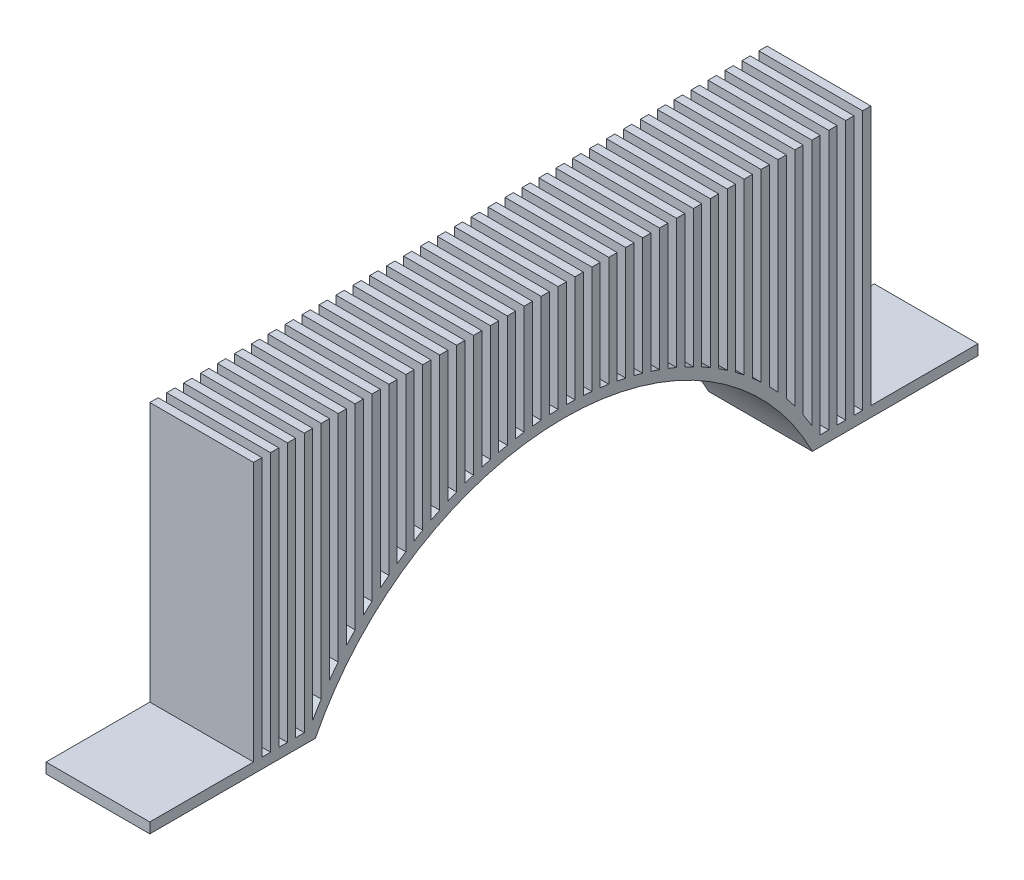
SolidWorks part; units mm, degrees
material "6061 Alloy"
ref_plane "Front Plane" through (0, 0, 0) normal (0, 0, 1) x (1, 0, 0)
ref_plane "Top Plane" through (0, 0, 0) normal (0, 1, 0) x (1, 0, 0)
ref_plane "Right Plane" through (0, 0, 0) normal (1, 0, 0) x (0, 0, -1)
sketch "Sketch1" plane through (0, 0, 0) normal (1, 0, 0) x (0, 0, -1)
  line L0 (18.792, 0) -> (29.9, 0)
  line L1 (-18.792, 0) -> (-29.9, 0)
  line L2 (-21.8, -11.05) -> (21.8, -11.05)
  line L3 (-29.9, 0) -> (-29.9, -11.05)
  line L4 (-29.9, -11.05) -> (-21.8, -11.05)
  line L5 (21.8, -11.05) -> (29.9, -11.05)
  line L6 (29.9, -11.05) -> (29.9, 0)
  line L7 (-29.9, 0) -> (-29.9, 1)
  line L8 (-29.9, 1) -> (-23.9382, 1)
  line L9 (23.9382, 1) -> (29.9, 1)
  line L10 (-24.5466, 2) -> (-39.9, 2)
  line L163 (-39.9, 2) -> (-39.9, 1)
  line L164 (-39.9, 1) -> (-23.9382, 1)
  line L165 (24.5466, 2) -> (39.9, 2)
  line L166 (29.9, 1) -> (29.9, 0)
  line L167 (39.9, 2) -> (39.9, 1)
  line L168 (39.9, 1) -> (23.9382, 1)
  line L169 (-28.27, 2) -> (-28.27, 27)
  line L174 (-29.9, 2) -> (-29.1, 2)
  line L175 (-29.9, 2) -> (-29.9, 27)
  line L176 (-29.9, 27) -> (-29.1, 27)
  line L177 (-29.1, 2) -> (-29.1, 27)
  line L178 (-28.27, 2) -> (-27.47, 2)
  line L179 (-27.47, 2) -> (-27.47, 27)
  line L180 (-28.27, 27) -> (-27.47, 27)
  line L181 (-26.64, 2) -> (-26.64, 27)
  line L182 (-26.64, 2) -> (-25.84, 2)
  line L183 (-25.84, 2) -> (-25.84, 27)
  line L184 (-26.64, 27) -> (-25.84, 27)
  line L185 (-25.01, 2) -> (-25.01, 27)
  line L186 (-25.01, 2) -> (-24.21, 2)
  line L187 (-24.21, 2) -> (-24.21, 27)
  line L188 (-25.01, 27) -> (-24.21, 27)
  line L189 (-23.38, 2) -> (-23.38, 27)
  line L190 (-23.38, 2) -> (-22.58, 2)
  line L191 (-22.58, 2) -> (-22.58, 27)
  line L192 (-23.38, 27) -> (-22.58, 27)
  line L193 (-21.75, 2) -> (-21.75, 27)
  line L194 (-21.75, 2) -> (-20.95, 2)
  line L195 (-20.95, 2) -> (-20.95, 27)
  line L196 (-21.75, 27) -> (-20.95, 27)
  line L197 (-20.12, 2) -> (-20.12, 27)
  line L198 (-20.12, 2) -> (-19.32, 2)
  line L199 (-19.32, 2) -> (-19.32, 27)
  line L200 (-20.12, 27) -> (-19.32, 27)
  line L201 (-18.49, 2) -> (-18.49, 27)
  line L202 (-18.49, 2) -> (-17.69, 2)
  line L203 (-17.69, 2) -> (-17.69, 27)
  line L204 (-18.49, 27) -> (-17.69, 27)
  line L205 (-16.86, 2) -> (-16.86, 27)
  line L206 (-16.86, 2) -> (-16.06, 2)
  line L207 (-16.06, 2) -> (-16.06, 27)
  line L208 (-16.86, 27) -> (-16.06, 27)
  line L209 (-15.23, 2) -> (-15.23, 27)
  line L210 (-15.23, 2) -> (-14.43, 2)
  line L211 (-14.43, 2) -> (-14.43, 27)
  line L212 (-15.23, 27) -> (-14.43, 27)
  line L213 (-13.6, 2) -> (-13.6, 27)
  line L214 (-13.6, 2) -> (-12.8, 2)
  line L215 (-12.8, 2) -> (-12.8, 27)
  line L216 (-13.6, 27) -> (-12.8, 27)
  line L217 (-11.97, 2) -> (-11.97, 27)
  line L218 (-11.97, 2) -> (-11.17, 2)
  line L219 (-11.17, 2) -> (-11.17, 27)
  line L220 (-11.97, 27) -> (-11.17, 27)
  line L221 (-10.34, 2) -> (-10.34, 27)
  line L222 (-10.34, 2) -> (-9.54, 2)
  line L223 (-9.54, 2) -> (-9.54, 27)
  line L224 (-10.34, 27) -> (-9.54, 27)
  line L225 (-8.71, 2) -> (-8.71, 27)
  line L226 (-8.71, 2) -> (-7.91, 2)
  line L227 (-7.91, 2) -> (-7.91, 27)
  line L228 (-8.71, 27) -> (-7.91, 27)
  line L229 (-7.08, 2) -> (-7.08, 27)
  line L230 (-7.08, 2) -> (-6.28, 2)
  line L231 (-6.28, 2) -> (-6.28, 27)
  line L232 (-7.08, 27) -> (-6.28, 27)
  line L233 (-5.45, 2) -> (-5.45, 27)
  line L234 (-5.45, 2) -> (-4.65, 2)
  line L235 (-4.65, 2) -> (-4.65, 27)
  line L236 (-5.45, 27) -> (-4.65, 27)
  line L237 (-3.82, 2) -> (-3.82, 27)
  line L238 (-3.82, 2) -> (-3.02, 2)
  line L239 (-3.02, 2) -> (-3.02, 27)
  line L240 (-3.82, 27) -> (-3.02, 27)
  line L241 (-2.19, 2) -> (-2.19, 27)
  line L242 (-2.19, 2) -> (-1.39, 2)
  line L243 (-1.39, 2) -> (-1.39, 27)
  line L244 (-2.19, 27) -> (-1.39, 27)
  line L245 (-0.56, 2) -> (-0.56, 27)
  line L246 (-0.56, 2) -> (0.24, 2)
  line L247 (0.24, 2) -> (0.24, 27)
  line L248 (-0.56, 27) -> (0.24, 27)
  line L249 (1.07, 2) -> (1.07, 27)
  line L250 (1.07, 2) -> (1.87, 2)
  line L251 (1.87, 2) -> (1.87, 27)
  line L252 (1.07, 27) -> (1.87, 27)
  line L253 (2.7, 2) -> (2.7, 27)
  line L254 (2.7, 2) -> (3.5, 2)
  line L255 (3.5, 2) -> (3.5, 27)
  line L256 (2.7, 27) -> (3.5, 27)
  line L257 (4.33, 2) -> (4.33, 27)
  line L258 (4.33, 2) -> (5.13, 2)
  line L259 (5.13, 2) -> (5.13, 27)
  line L260 (4.33, 27) -> (5.13, 27)
  line L261 (5.96, 2) -> (5.96, 27)
  line L262 (5.96, 2) -> (6.76, 2)
  line L263 (6.76, 2) -> (6.76, 27)
  line L264 (5.96, 27) -> (6.76, 27)
  line L265 (7.59, 2) -> (7.59, 27)
  line L266 (7.59, 2) -> (8.39, 2)
  line L267 (8.39, 2) -> (8.39, 27)
  line L268 (7.59, 27) -> (8.39, 27)
  line L269 (9.22, 2) -> (9.22, 27)
  line L270 (9.22, 2) -> (10.02, 2)
  line L271 (10.02, 2) -> (10.02, 27)
  line L272 (9.22, 27) -> (10.02, 27)
  line L273 (10.85, 2) -> (10.85, 27)
  line L274 (10.85, 2) -> (11.65, 2)
  line L275 (11.65, 2) -> (11.65, 27)
  line L276 (10.85, 27) -> (11.65, 27)
  line L277 (12.48, 2) -> (12.48, 27)
  line L278 (12.48, 2) -> (13.28, 2)
  line L279 (13.28, 2) -> (13.28, 27)
  line L280 (12.48, 27) -> (13.28, 27)
  line L281 (14.11, 2) -> (14.11, 27)
  line L282 (14.11, 2) -> (14.91, 2)
  line L283 (14.91, 2) -> (14.91, 27)
  line L284 (14.11, 27) -> (14.91, 27)
  line L285 (15.74, 2) -> (15.74, 27)
  line L286 (15.74, 2) -> (16.54, 2)
  line L287 (16.54, 2) -> (16.54, 27)
  line L288 (15.74, 27) -> (16.54, 27)
  line L289 (17.37, 2) -> (17.37, 27)
  line L290 (17.37, 2) -> (18.17, 2)
  line L291 (18.17, 2) -> (18.17, 27)
  line L292 (17.37, 27) -> (18.17, 27)
  line L293 (19, 2) -> (19, 27)
  line L294 (19, 2) -> (19.8, 2)
  line L295 (19.8, 2) -> (19.8, 27)
  line L296 (19, 27) -> (19.8, 27)
  line L297 (20.63, 2) -> (20.63, 27)
  line L298 (20.63, 2) -> (21.43, 2)
  line L299 (21.43, 2) -> (21.43, 27)
  line L300 (20.63, 27) -> (21.43, 27)
  line L301 (22.26, 2) -> (22.26, 27)
  line L302 (22.26, 2) -> (23.06, 2)
  line L303 (23.06, 2) -> (23.06, 27)
  line L304 (22.26, 27) -> (23.06, 27)
  line L305 (23.89, 2) -> (23.89, 27)
  line L306 (23.89, 2) -> (24.69, 2)
  line L307 (24.69, 2) -> (24.69, 27)
  line L308 (23.89, 27) -> (24.69, 27)
  line L309 (25.52, 2) -> (25.52, 27)
  line L310 (25.52, 2) -> (26.32, 2)
  line L311 (26.32, 2) -> (26.32, 27)
  line L312 (25.52, 27) -> (26.32, 27)
  line L313 (27.15, 2) -> (27.15, 27)
  line L314 (27.15, 2) -> (27.95, 2)
  line L315 (27.95, 2) -> (27.95, 27)
  line L316 (27.15, 27) -> (27.95, 27)
  line L317 (28.78, 2) -> (28.78, 27)
  line L318 (28.78, 2) -> (29.58, 2)
  line L319 (29.58, 2) -> (29.58, 27)
  line L320 (28.78, 27) -> (29.58, 27)
  arc A0 (21.8, -11.05) -> (-21.8, -11.05) centre (0, -11.05) ccw
  arc A3 (23.9382, 1) -> (-23.9382, 1) centre (0, -11.05) ccw
  arc A4 (23.3139, 0) -> (-23.3139, 0) centre (0, -11.05) ccw
  arc A5 (24.5466, 2) -> (-24.5466, 2) centre (0, -11.05) ccw
  point P47 (34.4187, -11.05)
  dimension "D1" = 21.8
  dimension "D5" = 25
  dimension "D10" = 1
  dimension "D7" = 0.8
  dimension "D11" = 1
  dimension "D2" = 11.05
  dimension "D3" = 8.1
  dimension "D4" = 8.1
  dimension "D6" = 1
  dimension "D8" = 1
  dimension "D12" = 10
  dimension "D9" = 1
  dimension "D13" = 10
  dimension "D14" = 37
extrude "Boss-Extrude1" add sketch "Sketch1" along normal blind 10 contours L184 L181 L10 L183 | A5 L195 L196 L193 | A5 L199 L200 L197 | A5 L203 L204 L201 | A5 L207 L208 L205 | A5 L211 L212 L209 | L10 L177 L176 L175 | A5 L187 L188 L185 L10 | A5 L191 L192 L189 | A5 L215 L216 L213 | A5 L219 L220 L217 | A5 L223 L224 L221 | A5 L227 L228 L225 | A5 L231 L232 L229 | A5 L235 L236 L233 | A5 L239 L240 L237 | A5 L243 L244 L241 | A5 L247 L248 L245 | A5 L251 L252 L249 | A5 L255 L256 L253 | A5 L259 L260 L257 | A5 L263 L264 L261 | A5 L267 L268 L265 | A5 L271 L272 L269 | A5 L275 L276 L273 | A5 L279 L280 L277 | A5 L283 L284 L281 | A5 L287 L288 L285 | A5 L291 L292 L289 | A5 L295 L296 L293 | A5 L299 L300 L297 | A5 L303 L304 L301 | A5 L165 L307 L308 L305 | L312 L309 L165 L311 | L316 L313 L165 L315 | L305 A5 L303 A3 L9 L168 L167 L165 L306 | L306 A5 L305 | L303 A5 L301 A3 | L301 A5 L299 A3 | L299 A5 L297 A3 | L297 A5 L295 A3 | L295 A5 L293 A3 | L293 A5 L291 A3 | L291 A5 L289 A3 | L289 A5 L287 A3 | L189 A5 L187 L186 L10 L163 L164 L8 A3 | L191 A5 L189 A3 | L187 A5 L186 | L193 A5 L191 A3 | L195 A5 L193 A3 | L197 A5 L195 A3 | L199 A5 L197 A3 | L201 A5 L199 A3 | L203 A5 L201 A3 | L205 A5 L203 A3 | L207 A5 L205 A3 | L209 A5 L207 A3 | L211 A5 L209 A3 | L213 A5 L211 A3 | L215 A5 L213 A3 | L217 A5 L215 A3 | L221 A5 L219 A3 | L223 A5 L221 A3 | L225 A5 L223 A3 | L227 A5 L225 A3 | L229 A5 L227 A3 | L231 A5 L229 A3 | L233 A5 L231 A3 | L235 A5 L233 A3 | L237 A5 L235 A3 | L239 A5 L237 A3 | L241 A5 L239 A3 | L243 A5 L241 A3 | L219 A5 L217 A3 | L245 A5 L243 A3 | L247 A5 L245 A3 | L249 A5 L247 A3 | L251 A5 L249 A3 | L253 A5 L251 A3 | L255 A5 L253 A3 | L257 A5 L255 A3 | L259 A5 L257 A3 | L261 A5 L259 A3 | L263 A5 L261 A3 | L265 A5 L263 A3 | L267 A5 L265 A3 | L269 A5 L267 A3 | L271 A5 L269 A3 | L273 A5 L271 A3 | L275 A5 L273 A3 | L277 A5 L275 A3 | L279 A5 L277 A3 | L281 A5 L279 A3 | L283 A5 L281 A3 | L285 A5 L283 A3 | L287 A5 L285 A3 | L317 L320 L319 L318 | L169 L180 L179 L178
